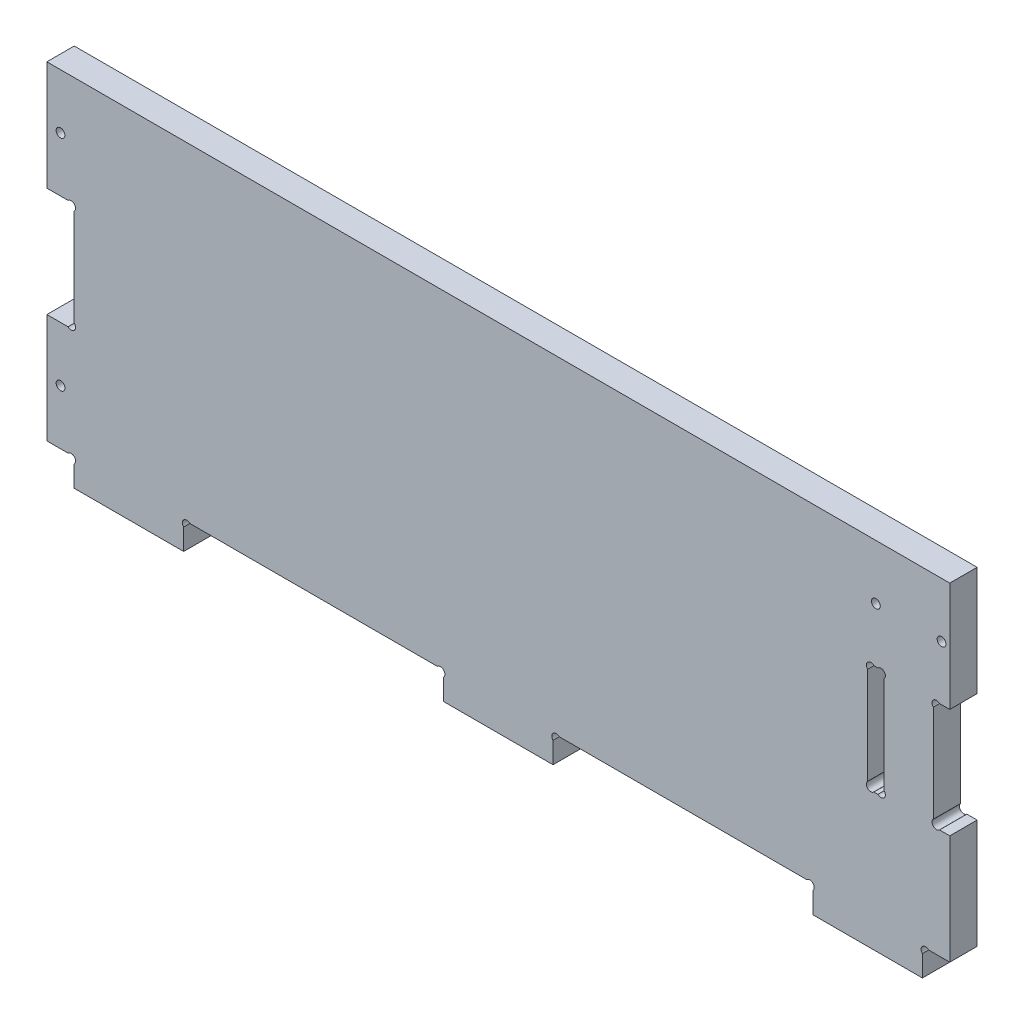
SolidWorks part; units mm, degrees
ref_plane "Plan de face" through (0, 0, 0) normal (0, 0, 1) x (1, 0, 0)
ref_plane "Plan de dessus" through (0, 0, 0) normal (0, 1, 0) x (1, 0, 0)
ref_plane "Plan de droite" through (0, 0, 0) normal (1, 0, 0) x (0, 0, -1)
sketch "Esquisse1" plane through (0, 0, 0) normal (0, 0, 1) x (1, 0, 0)
  line L0 (-81.6515, 0) -> (336.943, 0) construction
  line L1 (0, -7.0046) -> (0, 201.3745) construction
  line L2 (330, 201.3745) -> (330, -7.0046) construction
  line L3 (336.943, 130) -> (-81.6515, 130) construction
  line L4 (324, 147.7086) -> (324, 30.1101) construction
  line L5 (165, -7.0046) -> (165, 175.7082) construction
  line L6 (-24.2523, 10) -> (336.943, 10) construction
  line L7 (300, 30.1101) -> (300, 175.7082) construction
  line L8 (306, 30.1101) -> (306, 147.7086) construction
  line L9 (315, 159.3669) -> (315, 107.5758) construction
  line L10 (-50.8519, 70) -> (336.943, 70) construction
  line L11 (10, 147.7086) -> (10, -19.9717) construction
  line L12 (303, 82.1628) -> (303, 52.0341) construction
  line L13 (-50.8519, 50) -> (331.3802, 50) construction
  line L14 (306, 50) -> (292.3754, 63.6246) construction
  line L15 (302.2627, 50) -> (303.7373, 50)
  line L16 (326.2627, 50) -> (330, 50)
  line L17 (326.2627, 90) -> (330, 90)
  line L18 (302.2627, 90) -> (303.7373, 90)
  line L19 (10, 50) -> (-15.05, 75.05) construction
  line L20 (7.7373, 50) -> (0, 50)
  line L21 (7.7373, 90) -> (0, 90)
  line L22 (10, 87.7373) -> (10, 52.2627)
  line L23 (5, 35.3379) -> (5, -7.0046) construction
  line L24 (-24.2523, 30) -> (370.2645, 30) construction
  line L25 (30, -19.9717) -> (30, 35.3379) construction
  line L26 (10, 10) -> (-9.4788, -9.4788) construction
  line L27 (10, 7.7373) -> (10, 0)
  line L28 (50, 7.7373) -> (50, 0)
  line L29 (10, 0) -> (50, 0)
  line L30 (7.7373, 10) -> (0, 10)
  line L31 (322.2627, 10) -> (330, 10)
  line L32 (320, 0) -> (280, 0)
  line L33 (280, 7.7373) -> (280, 0)
  line L34 (320, 7.7373) -> (320, 0)
  line L35 (280, -28.8) -> (280, 19.4852) construction
  line L36 (232.5, -28.8) -> (232.5, 19.4852) construction
  line L37 (185, 7.7373) -> (185, 0)
  line L38 (145, 7.7373) -> (145, 0)
  line L39 (324, 87.7373) -> (324, 52.2627)
  line L40 (306, 52.2627) -> (306, 87.7373)
  line L41 (300, 87.7373) -> (300, 52.2627)
  line L42 (330, 10) -> (330, 50)
  line L43 (330, 90) -> (330, 130)
  line L44 (330, 130) -> (0, 130)
  line L45 (0, 130) -> (0, 90)
  line L46 (0, 50) -> (0, 10)
  line L47 (52.2627, 10) -> (142.7373, 10)
  line L48 (145, 0) -> (185, 0)
  line L49 (187.2627, 10) -> (277.7373, 10)
  line L50 (327, 35.3379) -> (327, 19.4852) construction
  arc A0 (303.7373, 50) -> (306, 52.2627) centre (304.8686, 51.1314) ccw
  arc A1 (302.2627, 50) -> (300, 52.2627) centre (301.1314, 51.1314) cw
  arc A2 (303.7373, 90) -> (306, 87.7373) centre (304.8686, 88.8686) cw
  arc A3 (302.2627, 90) -> (300, 87.7373) centre (301.1314, 88.8686) ccw
  arc A4 (326.2627, 50) -> (324, 52.2627) centre (325.1314, 51.1314) cw
  arc A5 (326.2627, 90) -> (324, 87.7373) centre (325.1314, 88.8686) ccw
  arc A6 (7.7373, 50) -> (10, 52.2627) centre (8.8686, 51.1314) ccw
  arc A7 (7.7373, 90) -> (10, 87.7373) centre (8.8686, 88.8686) cw
  circle A8 centre (5, 30) radius 1.6
  circle A9 centre (5, 110) radius 1.6
  arc A10 (10, 7.7373) -> (7.7373, 10) centre (8.8686, 8.8686) ccw
  arc A11 (50, 7.7373) -> (52.2627, 10) centre (51.1314, 8.8686) cw
  arc A12 (280, 7.7373) -> (277.7373, 10) centre (278.8686, 8.8686) ccw
  arc A13 (320, 7.7373) -> (322.2627, 10) centre (321.1314, 8.8686) cw
  arc A14 (185, 7.7373) -> (187.2627, 10) centre (186.1314, 8.8686) cw
  arc A15 (145, 7.7373) -> (142.7373, 10) centre (143.8686, 8.8686) ccw
  circle A17 centre (327, 110) radius 1.6
  circle A18 centre (303, 110) radius 1.6
  dimension "D14" = 45
  dimension "D15" = 5
  dimension "D17" = 20
  dimension "D19" = 47.5
  dimension "D1" = 330
  dimension "D2" = 130
  dimension "D3" = 60
  dimension "D4" = 165
  dimension "D5" = 15
  dimension "D6" = 6
  dimension "D7" = 6
  dimension "D8" = 30
  dimension "D9" = 10
  dimension "D10" = 10
  dimension "D11" = 3
  dimension "D12" = 20
  dimension "D13" = 45
  dimension "D16" = 20
  dimension "D18" = 45
  dimension "D20" = 3
extrude "Extrusion1" add sketch "Esquisse1" along normal blind 10
